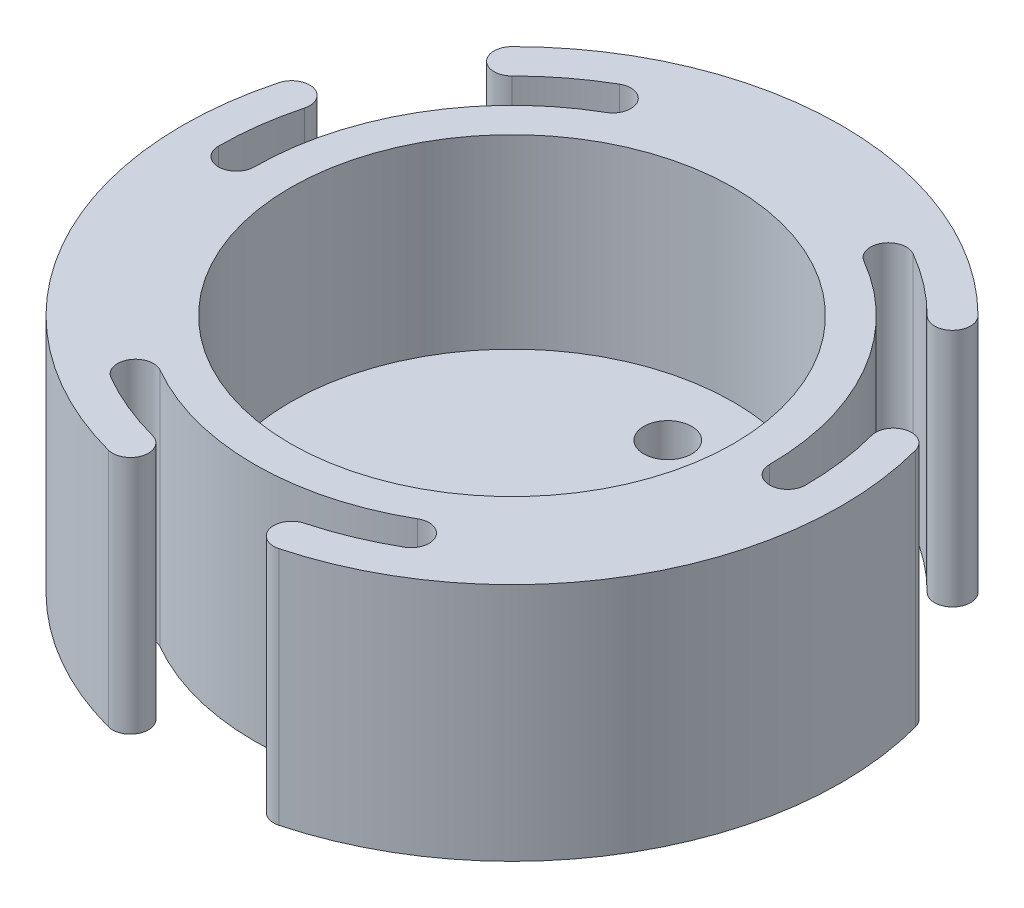
SolidWorks part; units mm, degrees
material "Alliage 1060"
ref_plane "Plan de face" through (0, 0, 0) normal (0, 0, 1) x (1, 0, 0)
ref_plane "Plan de dessus" through (0, 0, 0) normal (0, 1, 0) x (1, 0, 0)
ref_plane "Plan de droite" through (0, 0, 0) normal (1, 0, 0) x (0, 0, -1)
sketch "Esquisse1" plane through (0, 0, 0) normal (0, 1, 0) x (1, 0, 0)
  circle A0 centre (0, 0) radius 18.5
  circle A1 centre (0, 0) radius 30 construction
  circle A2 centre (0, 0) radius 27 construction
  circle A3 centre (0, 0) radius 24.5
  circle A4 centre (0, 0) radius 21.5 construction
  dimension "D1" = 37
  dimension "D2" = 60
  dimension "D3" = 54
  dimension "D4" = 49
  dimension "D5" = 43
extrude "Boss.-Extru.1" add sketch "Esquisse1" along normal blind 20
sketch "Esquisse2" plane through (0, 20, 0) normal (0, 1, 0) x (1, 0, 0)
  line L0 (-11.5, 19.9186) -> (0, 0) construction
  line L1 (0, 0) -> (-23, 0) construction
  line L2 (0, 0) -> (0, 24.5) construction
  arc A0 (-23, 0) -> (-11.5, 19.9186) centre (0, 0) cw construction
  arc A1 (-12.25, 21.2176) -> (-24.5, 0) centre (0, 0) ccw
  arc A2 (-10.75, 18.6195) -> (-21.5, 0) centre (0, 0) ccw
  arc A3 (-10.75, 18.6195) -> (-12.25, 21.2176) centre (-11.5, 19.9186) ccw
  arc A4 (-24.5, 0) -> (-21.5, 0) centre (-23, 0) ccw
  circle A5 centre (0, 0) radius 24.5 construction
  arc A6 (11.5, 19.9186) -> (23, 0) centre (0, 0) cw construction
  arc A7 (24.5, 0) -> (12.25, 21.2176) centre (0, 0) ccw
  arc A8 (21.5, 0) -> (10.75, 18.6195) centre (0, 0) ccw
  arc A9 (21.5, 0) -> (24.5, 0) centre (23, 0) ccw
  arc A10 (12.25, 21.2176) -> (10.75, 18.6195) centre (11.5, 19.9186) ccw
  arc A11 (11.5, -19.9186) -> (-11.5, -19.9186) centre (0, 0) cw construction
  arc A12 (-12.25, -21.2176) -> (12.25, -21.2176) centre (0, 0) ccw
  arc A13 (-10.75, -18.6195) -> (10.75, -18.6195) centre (0, 0) ccw
  arc A14 (-10.75, -18.6195) -> (-12.25, -21.2176) centre (-11.5, -19.9186) ccw
  arc A15 (12.25, -21.2176) -> (10.75, -18.6195) centre (11.5, -19.9186) ccw
  point P4 (-19.9186, 11.5)
  point P21 (19.9186, 11.5)
  point P28 (0, -23)
  point P33 (0, 0)
  dimension "D1" = 1.5
  dimension "D2" = 60
  dimension "D3" = 30
extrude "Enlèv. mat.-Extru.1" cut sketch "Esquisse2" against normal through all
sketch "Esquisse3" plane through (0, 20, 0) normal (0, 1, 0) x (1, 0, 0)
  line L0 (0, 26) -> (0, 0) construction
  line L1 (-18.3848, 18.3848) -> (0, 0) construction
  arc A0 (-18.3848, 18.3848) -> (18.3848, 18.3848) centre (0, 0) cw construction
  arc A1 (19.4454, 19.4454) -> (-19.4454, 19.4454) centre (0, 0) ccw
  arc A2 (17.3241, 17.3241) -> (-17.3241, 17.3241) centre (0, 0) ccw
  arc A3 (17.3241, 17.3241) -> (19.4454, 19.4454) centre (18.3848, 18.3848) ccw
  arc A4 (-19.4454, 19.4454) -> (-17.3241, 17.3241) centre (-18.3848, 18.3848) ccw
  arc A5 (12.25, 21.2176) -> (-12.25, 21.2176) centre (0, 0) ccw construction
  arc A6 (25.1141, 6.7293) -> (6.7293, -25.1141) centre (0, 0) cw construction
  arc A7 (7.1175, -26.563) -> (26.563, 7.1175) centre (0, 0) ccw
  arc A8 (6.3411, -23.6652) -> (23.6652, 6.3411) centre (0, 0) ccw
  arc A9 (6.3411, -23.6652) -> (7.1175, -26.563) centre (6.7293, -25.1141) ccw
  arc A10 (26.563, 7.1175) -> (23.6652, 6.3411) centre (25.1141, 6.7293) ccw
  arc A11 (-6.7293, -25.1141) -> (-25.1141, 6.7293) centre (0, 0) cw construction
  arc A12 (-26.563, 7.1175) -> (-7.1175, -26.563) centre (0, 0) ccw
  arc A13 (-23.6652, 6.3411) -> (-6.3411, -23.6652) centre (0, 0) ccw
  arc A14 (-23.6652, 6.3411) -> (-26.563, 7.1175) centre (-25.1141, 6.7293) ccw
  arc A15 (-7.1175, -26.563) -> (-6.3411, -23.6652) centre (-6.7293, -25.1141) ccw
  point P4 (0, 26)
  point P19 (22.5167, -13)
  point P26 (-22.5167, -13)
  point P31 (0, 0)
  dimension "D1" = 1.5
  dimension "D2" = 45
extrude "Boss.-Extru.2" add sketch "Esquisse3" against normal up to surface (20 mm away) up to face at (0, 0, 0)
sketch "Esquisse4" plane through (0, 0, 0) normal (0, -1, 0) x (1, 0, 0)
  circle A0 centre (0, 0) radius 21.5
  arc A1 (10.75, 18.6195) -> (-10.75, 18.6195) centre (0, 0) ccw construction
extrude "Boss.-Extru.3" add sketch "Esquisse4" against normal blind 4.5
sketch "Esquisse5" plane through (0, 4.5, 0) normal (0, 1, 0) x (1, 0, 0)
  line L0 (0, 0) -> (0, 13) construction
  circle A0 centre (0, 13) radius 2
  circle A1 centre (11.2583, -6.5) radius 2
  circle A2 centre (-11.2583, -6.5) radius 2
  point P12 (0, 0)
  dimension "D2" = 4
  dimension "D1" = 13
  dimension "D3" = 3
extrude "Enlèv. mat.-Extru.2" cut sketch "Esquisse5" against normal up to next
